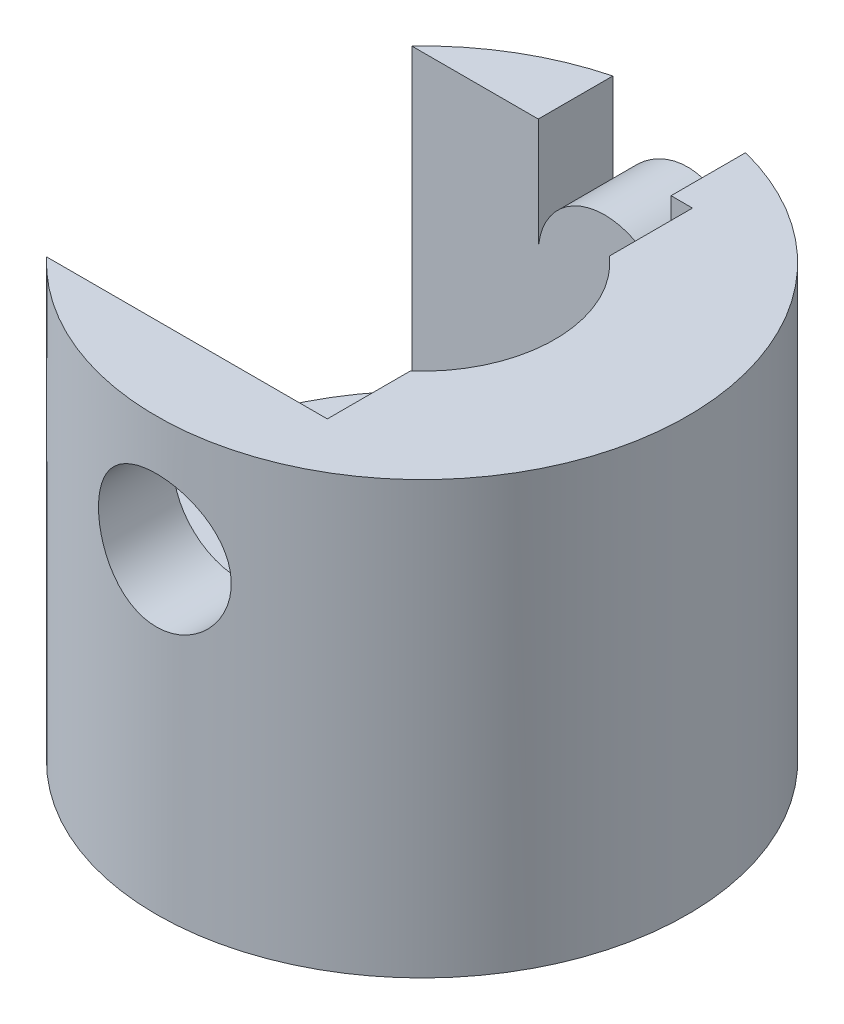
SolidWorks part; units mm, degrees
ref_plane "前视基准面" through (0, 0, 0) normal (0, 0, 1) x (1, 0, 0)
ref_plane "上视基准面" through (0, 0, 0) normal (0, 1, 0) x (1, 0, 0)
ref_plane "右视基准面" through (0, 0, 0) normal (1, 0, 0) x (0, 0, -1)
sketch "草图1" plane through (0, 0, 0) normal (0, 1, 0) x (1, 0, 0)
  circle A0 centre (0, 0) radius 80
  dimension "D1" = 160
extrude "凸台-拉伸1" add sketch "草图1" along normal blind 130
sketch "草图2" plane through (0, 0, 0) normal (0, -1, 0) x (1, 0, 0)
  circle A0 centre (0, 0) radius 40
  dimension "D1" = 80
extrude "切除-拉伸1" cut sketch "草图2" against normal blind 40
sketch "草图3" plane through (0, 40, 0) normal (0, -1, 0) x (1, 0, 0)
  line L0 (-58.0948, 55) -> (26.4575, 55)
  line L1 (26.4575, 55) -> (26.4575, 30)
  line L3 (26.4575, -55) -> (26.4575, -30)
  line L4 (-58.0948, -55) -> (26.4575, -55)
  line L5 (0, 0) -> (40, 0) construction
  arc A0 (26.4575, -30) -> (26.4575, 30) centre (0, 0) ccw
  circle A1 centre (0, 0) radius 80 construction
  circle A2 centre (0, 0) radius 40 construction
  arc A3 (-58.0948, -55) -> (-58.0948, 55) centre (0, 0) cw
  dimension "D1" = 55
  dimension "D2" = 30
extrude "切除-拉伸3" cut sketch "草图3" against normal blind 90
sketch "草图4" plane through (0, 0, 0) normal (0, 0, 1) x (1, 0, 0)
  circle A0 centre (0, 95) radius 20
  dimension "D1" = 95
extrude "切除-拉伸4" cut sketch "草图4" along direction (0, 0, 1) on the side of the normal through all both and the other way through all
sketch "草图7" plane through (0, 130, 0) normal (0, 1, 0) x (1, 0, 0)
  line L5 (0, 0) -> (40, 0) construction
  line L6 (20, 55) -> (-20, 55)
  line L7 (20, 77.4597) -> (20, 55)
  line L8 (-20, 55) -> (-20, 77.4597)
  arc A2 (26.4575, -30) -> (26.4575, 30) centre (0, 0) ccw construction
  arc A3 (20, 77.4597) -> (-20, 77.4597) centre (0, 0) ccw
sketch "草图8" plane through (0, 0, -55) normal (0, 0, 1) x (1, 0, 0)
  circle A0 centre (0, 95) radius 20
extrude "切除-拉伸8" cut sketch "草图7" against normal up to surface (35 mm away) up to face at (-20, 95, -55)
extrude "凸台-拉伸5" add sketch "草图8" against normal up to surface (22.4597 mm away)
